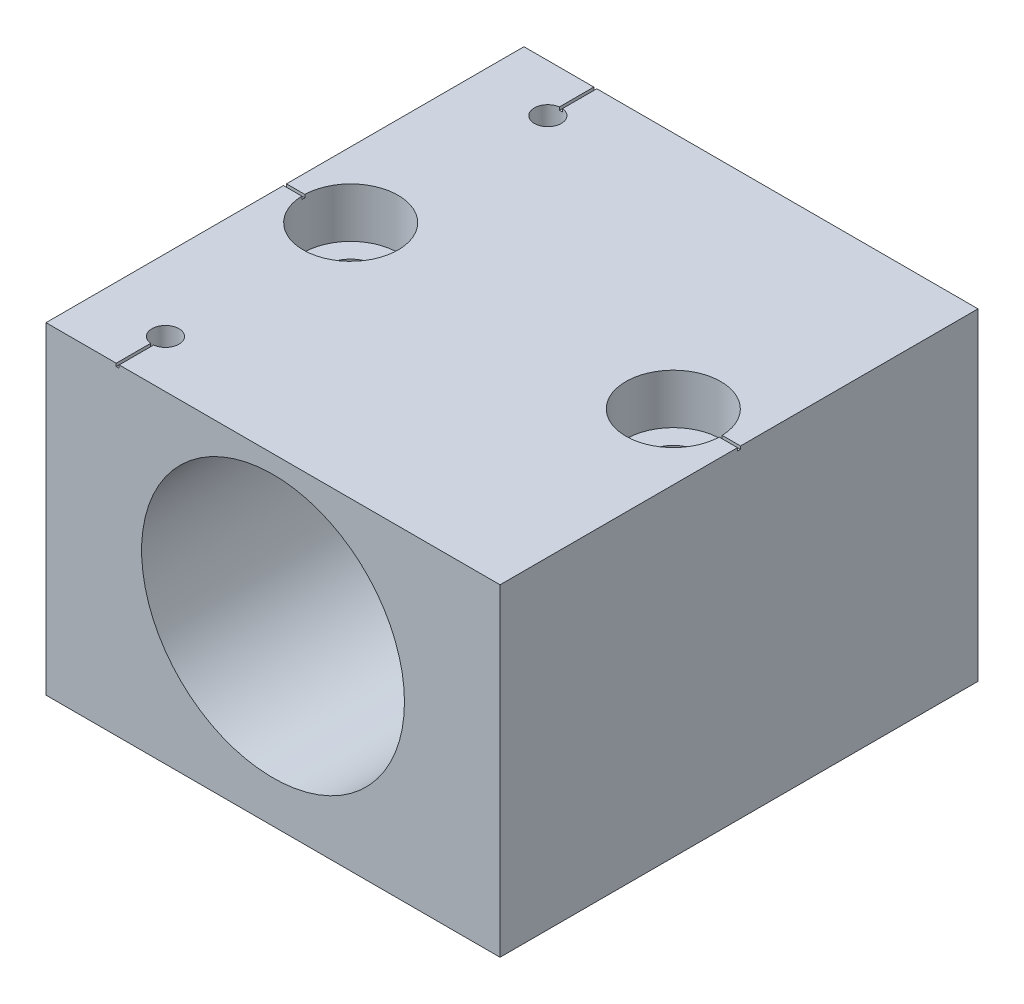
SolidWorks part; units mm, degrees
material "6061 Alloy"
ref_plane "Front" through (0, 0, 0) normal (0, 0, 1) x (1, 0, 0)
ref_plane "Top" through (0, 0, 0) normal (0, 1, 0) x (1, 0, 0)
ref_plane "Right" through (0, 0, 0) normal (1, 0, 0) x (0, 0, -1)
sketch "Sketch1" plane through (0, 0, 0) normal (0, 0, 1) x (1, 0, 0)
  line L1 (-19, 0) -> (19, 0)
  line L2 (-19, 0) -> (-19, 27)
  line L3 (-19, 27) -> (19, 27)
  line L4 (19, 0) -> (19, 27)
  dimension "D1" = 38
  dimension "D2" = 27
extrude "Extrude1" add sketch "Sketch1" along normal mid plane 40
sketch "Sketch2" plane through (0, 0, 0) normal (0, 0, 1) x (1, 0, 0)
  line L0 (-19, 0) -> (19, 0) construction
  circle A0 centre (0, 14.5) radius 11
  dimension "D1" = 22
  dimension "D2" = 14.5
extrude "Light-Weighting Hole" cut sketch "Sketch2" against normal through all and the other way through all
hole_wizard "#4-40 Tapped Hole1" positions "Sketch5" profile "Sketch4" tap size "#4-40" standard "Ansi Inch"
sketch "Sketch5" plane through (0, 27, 0) normal (0, 1, 0) x (-1, 0, 0)
  line L0 (16.0382, 0) -> (-10.3234, 0) construction
  line L1 (19, 20) -> (19, -20) construction
  point P0 (13, -16)
  point P1 (13, 16)
  dimension "D1" = 32
  dimension "D2" = 6
sketch "Sketch4" plane through (-13, 27, -16) normal (1, 0, 0) x (0, 0, 1)
  line L0 (0, 0) -> (0, 9.5438)
  line L1 (0, 9.5438) -> (1.1303, 8.8646)
  line L2 (1.1303, 8.8646) -> (1.1303, 0)
  line L5 (1.1303, 0) -> (0, 0)
  line L10 (0, 9.5438) -> (-1.1303, 8.8646) construction
  line L11 (0, -6.35) -> (0, 107.95) construction
  dimension "Tap Drill Dia." = 2.2606
  dimension "Tap Drill Depth" = 8.8646
  dimension "Drill Angle" = 118
cosmetic thread "Cosmetic Thread1" parameters "D1"=5.6896, "D2"=2.8448
cosmetic thread "Cosmetic Thread2" parameters "D1"=5.6896, "D2"=2.8448
hole_wizard "CBORE for #8 Socket Head Cap Screw1" positions "Sketch8" profile "Sketch7" counterbore size "#8" standard "Ansi Inch" end condition through all
sketch "Sketch8" plane through (0, 27, 0) normal (0, 1, 0) x (-1, 0, 0)
  line L0 (13.5, 0) -> (-13.5, 0) construction
  line L1 (0, -10.8765) -> (0, 13.4573) construction
  point P0 (13.5, 0)
  point P1 (-13.5, 0)
  dimension "D1" = 27
sketch "Sketch7" plane through (-13.5, 27, 0) normal (1, 0, 0) x (0, 0, 1)
  line L0 (0, 0) -> (0, 27)
  line L1 (0, 27) -> (2.1526, 27)
  line L3 (2.1526, 27) -> (2.1526, 4.1656)
  line L4 (2.1526, 4.1656) -> (3.9687, 4.1656)
  line L5 (3.9687, 4.1656) -> (3.9687, 0)
  line L7 (3.9687, 0) -> (0, 0)
  line L11 (0, -6.35) -> (0, 107.95) construction
  dimension "Thru Hole Dia." = 4.3053
  dimension "Thru Hole Depth" = 27
  dimension "C'Bore Dia." = 7.9375
  dimension "C'Bore Depth" = 4.1656
sketch "Sketch9" plane through (0, 27, 0) normal (0, 1, 0) x (-1, 0, 0)
  line L0 (-19, -20) -> (19, -20) construction
  line L1 (13.1515, -20) -> (12.9015, -20)
  line L2 (13.1515, -20) -> (13.1515, -16)
  line L3 (13.1515, -16) -> (12.9015, -16)
  line L4 (12.9015, -20) -> (12.9015, -16)
  line L5 (-19, 20) -> (19, 20) construction
  line L6 (13.1231, 20) -> (12.8731, 20)
  line L7 (13.1231, 20) -> (13.1231, 16)
  line L8 (13.1231, 16) -> (12.8731, 16)
  line L9 (12.8731, 20) -> (12.8731, 16)
  line L10 (-19, 20) -> (-19, -20) construction
  line L11 (-19, -0.125) -> (-16.9976, -0.125)
  line L12 (-19, -0.125) -> (-19, 0.125)
  line L13 (-19, 0.125) -> (-16.9976, 0.125)
  line L14 (-16.9976, -0.125) -> (-16.9976, 0.125)
  line L15 (19, 20) -> (19, -20) construction
  line L16 (2.9708, 0) -> (-2.4807, 0) construction
  line L17 (19, -0.125) -> (16.8751, -0.125)
  line L18 (19, -0.125) -> (19, 0.125)
  line L19 (19, 0.125) -> (16.8751, 0.125)
  line L20 (16.8751, -0.125) -> (16.8751, 0.125)
  dimension "D1" = 0.25
  dimension "D2" = 0.25
  dimension "D3" = 0.25
  dimension "D4" = 0.25
extrude "Cut-Extrude1" cut sketch "Sketch9" against normal blind 0.25
